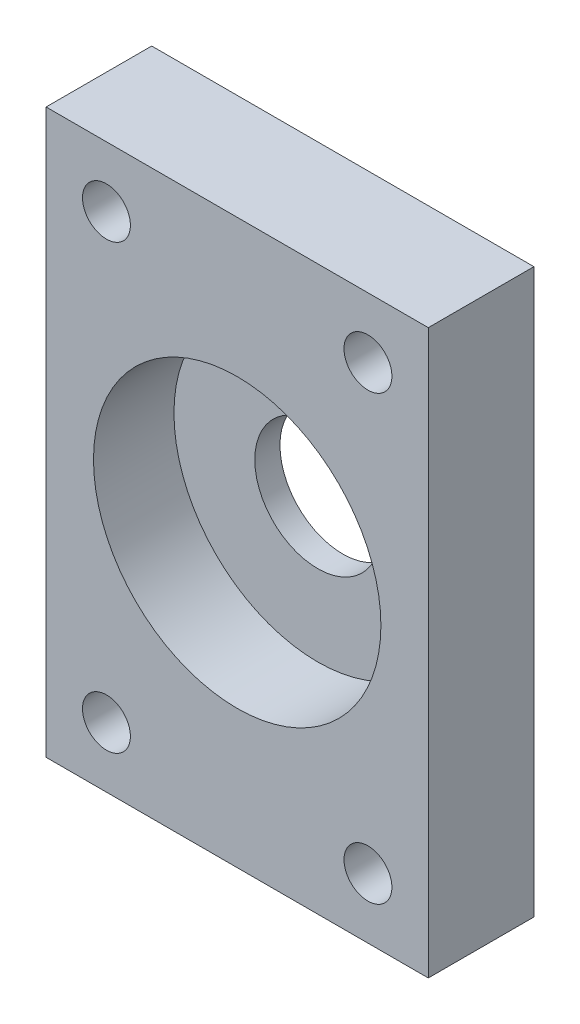
SolidWorks part; units mm, degrees
ref_plane "Alzado" through (0, 0, 0) normal (0, 0, 1) x (1, 0, 0)
ref_plane "Planta" through (0, 0, 0) normal (0, 1, 0) x (1, 0, 0)
ref_plane "Vista lateral" through (0, 0, 0) normal (1, 0, 0) x (0, 0, -1)
sketch "Croquis1" plane through (0, 0, 0) normal (0, 0, 1) x (1, 0, 0)
  circle A0 centre (0, 0) radius 14.2875
  circle A1 centre (0, 0) radius 18.2875
  dimension "D1" = 28.575
  dimension "D2" = 4
extrude "Saliente-Extruir1" add sketch "Croquis1" along normal blind 8 contours A1
sketch "Croquis2" plane through (0, 0, 0) normal (0, 0, -1) x (-1, 0, 0)
  line L1 (-19, -28) -> (19, -28)
  line L2 (-19, -28) -> (-19, 28)
  line L3 (-19, 28) -> (19, 28)
  line L4 (19, -28) -> (19, 28)
  line L5 (-19, -28) -> (19, 28) construction
  line L6 (-19, 28) -> (19, -28) construction
  circle A0 centre (0, 0) radius 18.2875 construction
  circle A1 centre (0, 0) radius 18.2875
  point P0 (0, 0)
  dimension "D1" = 38
  dimension "D2" = 56
extrude "Saliente-Extruir2" add sketch "Croquis2" against normal blind 8
sketch "Croquis5" plane through (0, 0, 0) normal (0, 0, -1) x (-1, 0, 0)
  line L4 (19, -28) -> (19, 28)
  line L5 (19, 28) -> (-19, 28)
  line L6 (-19, 28) -> (-19, -28)
  line L7 (-19, -28) -> (19, -28)
  line L8 (19, -28) -> (19, 28)
  line L9 (19, 28) -> (-19, 28)
  line L10 (-19, 28) -> (-19, -28)
  line L11 (-19, -28) -> (19, -28)
  circle A0 centre (0, 0) radius 6.25
  dimension "D2" = 12.5
  dimension "D1" = 0
extrude "Saliente-Extruir3" add sketch "Croquis5" along normal blind 2.5
sketch "Croquis7" plane through (0, 0, -2.5) normal (0, 0, -1) x (-1, 0, 0)
  line L0 (25.83, 0) -> (-30.4698, 0) construction
  line L1 (0, 25.0731) -> (0, -24.2875) construction
  line L2 (19, 28) -> (-19, 28) construction
  line L3 (-19, 28) -> (-19, -28) construction
  circle A0 centre (-13, 22) radius 2.3813
  circle A1 centre (13, 22) radius 2.3813
  circle A2 centre (13, -22) radius 2.3813
  circle A3 centre (-13, -22) radius 2.3813
  dimension "D3" = 4.7625
  dimension "D1" = 6
  dimension "D2" = 6
extrude "Cortar-Extruir3" cut sketch "Croquis7" against normal through all
